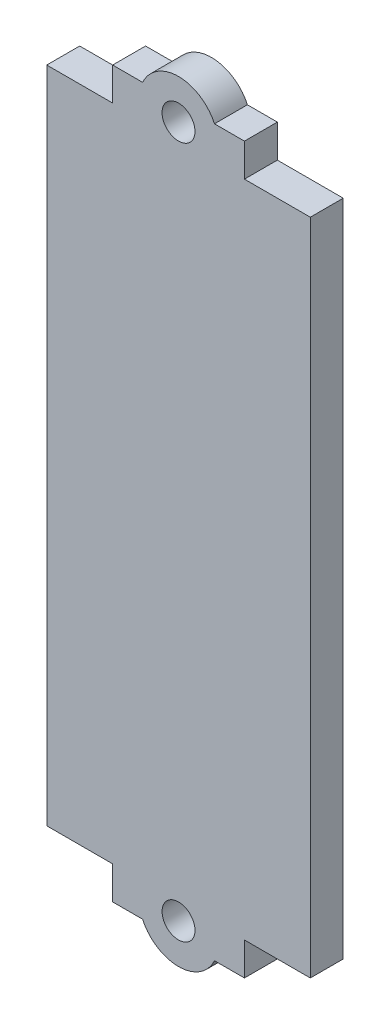
SolidWorks part; units mm, degrees
ref_plane "Front Plane" through (0, 0, 0) normal (0, 0, 1) x (1, 0, 0)
ref_plane "Top Plane" through (0, 0, 0) normal (0, 1, 0) x (1, 0, 0)
ref_plane "Right Plane" through (0, 0, 0) normal (1, 0, 0) x (0, 0, -1)
sketch "Sketch1" plane through (0, 0, 0) normal (0, 0, 1) x (1, 0, 0)
  line L1 (20, 50) -> (-20, 50)
  line L2 (20, 50) -> (20, -50)
  line L3 (20, -50) -> (-20, -50)
  line L4 (-20, 50) -> (-20, -50)
  line L5 (20, 50) -> (-20, -50) construction
  line L6 (20, -50) -> (-20, 50) construction
  point P0 (0, 0)
  dimension "D1" = 40
  dimension "D2" = 100
extrude "Boss-Extrude1" add sketch "Sketch1" along normal blind 5
sketch "Sketch2" plane through (0, 50, 0) normal (0, 1, 0) x (1, 0, 0)
  line L0 (20, -5) -> (-20, -5) construction
  line L1 (-10, -5) -> (10, -5)
  line L2 (-10, -5) -> (-10, 0)
  line L3 (-10, 0) -> (10, 0)
  line L4 (10, -5) -> (10, 0)
  line L5 (20, 0) -> (-20, 0) construction
  line L6 (-20, -5) -> (-20, 0) construction
  line L8 (20, -5) -> (20, 0) construction
  dimension "D1" = 10
  dimension "D2" = 20
  dimension "D3" = 10
  dimension "D4" = 5
extrude "Boss-Extrude2" add sketch "Sketch2" along normal blind 5
mirror "Mirror1" about plane through (0, 0, 0) normal (0, 1, 0) of "Boss-Extrude2"
sketch "Sketch3" plane through (0, 0, 5) normal (0, 0, 1) x (1, 0, 0)
  line L0 (-10, 55) -> (10, 55) construction
  line L1 (-10, 50) -> (-20, 50) construction
  line L2 (10, 55) -> (10, 50) construction
  line L3 (-10, 55) -> (-10, 50) construction
  circle A0 centre (0, 52.5) radius 6
  dimension "D1" = 12
  dimension "D2" = 2.5
  dimension "D3" = 10
  dimension "D4" = 2.5
  dimension "D5" = 10
extrude "Boss-Extrude3" add sketch "Sketch3" against normal blind 5
sketch "Sketch4" plane through (0, 0, 5) normal (0, 0, 1) x (1, 0, 0)
  line L0 (10, 55) -> (10, 50) construction
  line L1 (5.4544, 55) -> (10, 55) construction
  circle A0 centre (0, 52.5) radius 2.5
  arc A2 (5.4544, 55) -> (-5.4544, 55) centre (0, 52.5) ccw construction
  dimension "D1" = 5
  dimension "D2" = 10
  dimension "D3" = 2.5
  dimension "D4" = 3.5
extrude "Cut-Extrude1" cut sketch "Sketch4" against normal blind 5
mirror "Mirror2" about plane through (0, 0, 0) normal (0, 1, 0) of "Boss-Extrude3", "Cut-Extrude1"
